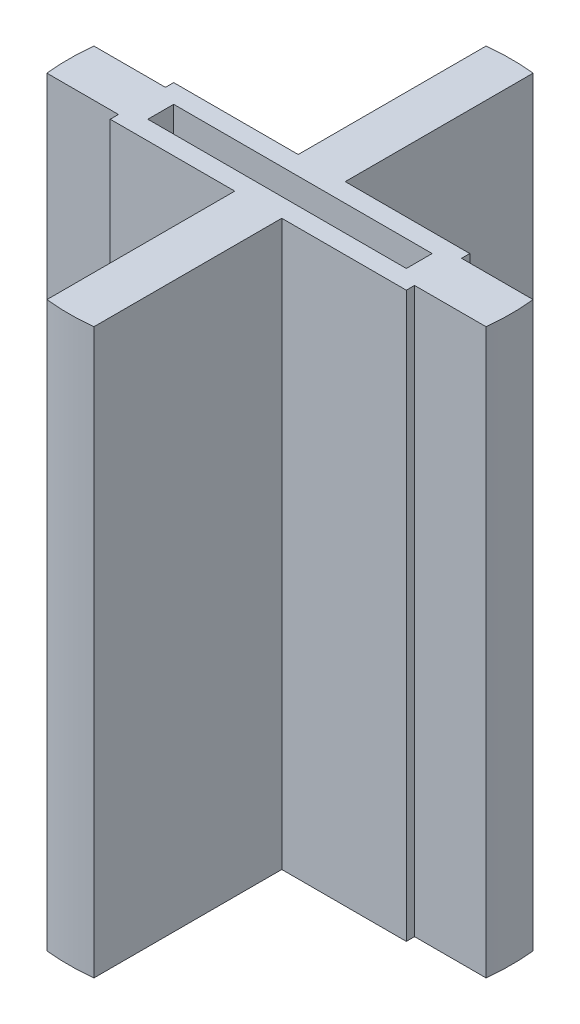
SolidWorks part; units mm, degrees
ref_plane "Front Plane" through (0, 0, 0) normal (0, 0, 1) x (1, 0, 0)
ref_plane "Top Plane" through (0, 0, 0) normal (0, 1, 0) x (1, 0, 0)
ref_plane "Right Plane" through (0, 0, 0) normal (1, 0, 0) x (0, 0, -1)
sketch "Sketch1" plane through (0, 0, 0) normal (0, 1, 0) x (1, 0, 0)
  line L1 (-34.925, -3.4925) -> (34.925, -3.4925)
  line L2 (-34.925, -3.4925) -> (-34.925, 3.4925)
  line L3 (-34.925, 3.4925) -> (34.925, 3.4925)
  line L4 (34.925, -3.4925) -> (34.925, 3.4925)
  line L5 (-34.925, -3.4925) -> (34.925, 3.4925) construction
  line L6 (-34.925, 3.4925) -> (34.925, -3.4925) construction
  line L7 (40.005, 8.5725) -> (-40.005, 8.5725)
  line L8 (40.005, 8.5725) -> (40.005, -8.5725)
  line L9 (40.005, -8.5725) -> (-40.005, -8.5725)
  line L10 (-40.005, 8.5725) -> (-40.005, -8.5725)
  line L11 (40.005, 8.5725) -> (-40.005, -8.5725) construction
  line L12 (40.005, -8.5725) -> (-40.005, 8.5725) construction
  line L13 (-6.35, -59.3513) -> (6.35, -59.3513)
  line L14 (-6.35, -59.3513) -> (-6.35, 59.3513)
  line L15 (-6.35, 59.3513) -> (6.35, 59.3513)
  line L16 (6.35, -59.3513) -> (6.35, 59.3513)
  line L17 (-6.35, -59.3513) -> (6.35, 59.3513) construction
  line L18 (-6.35, 59.3513) -> (6.35, -59.3513) construction
  line L19 (-59.3513, 6.35) -> (59.3513, 6.35)
  line L20 (-59.3513, 6.35) -> (-59.3513, -6.35)
  line L21 (-59.3513, -6.35) -> (59.3513, -6.35)
  line L22 (59.3513, 6.35) -> (59.3513, -6.35)
  line L23 (-59.3513, 6.35) -> (59.3513, -6.35) construction
  line L24 (-59.3513, -6.35) -> (59.3513, 6.35) construction
  circle A0 centre (0, 0) radius 59.69
  point P0 (0, 0)
  point P6 (0, 0)
  dimension "D5" = 119.38
  dimension "D1" = 6.985
  dimension "D2" = 69.85
  dimension "D3" = 5.08
  dimension "D4" = 5.08
  dimension "D6" = 12.7
  dimension "D7" = 12.7
extrude "Boss-Extrude1" add sketch "Sketch1" along normal mid plane 152.4 contours L20 L21 L10 L19 | L20 A0 | L21 L10 L9 L14 | L10 L21 L14 L1 L2 L3 L19 | L10 L19 L14 L7 | L14 L19 L16 L7 | L19 L14 L3 L16 | L16 L19 L8 L7 | L16 L21 L8 L19 L3 L4 L1 | L21 L16 L9 L8 | L21 L14 L9 L16 | L14 L21 L16 L1 | L13 L16 L9 L14 | L13 A0 | L22 L19 L8 L21 | L22 A0 | L7 L16 L15 L14 | L15 A0
sketch "Sketch2" plane through (0, -76.2, 0) normal (0, -1, 0) x (1, 0, 0)
  line L1 (-40.005, 8.5725) -> (40.005, 8.5725)
  line L2 (-40.005, 8.5725) -> (-40.005, -8.5725)
  line L3 (-40.005, -8.5725) -> (40.005, -8.5725)
  line L4 (40.005, 8.5725) -> (40.005, -8.5725)
extrude "Boss-Extrude2" add sketch "Sketch2" against normal blind 6.35
